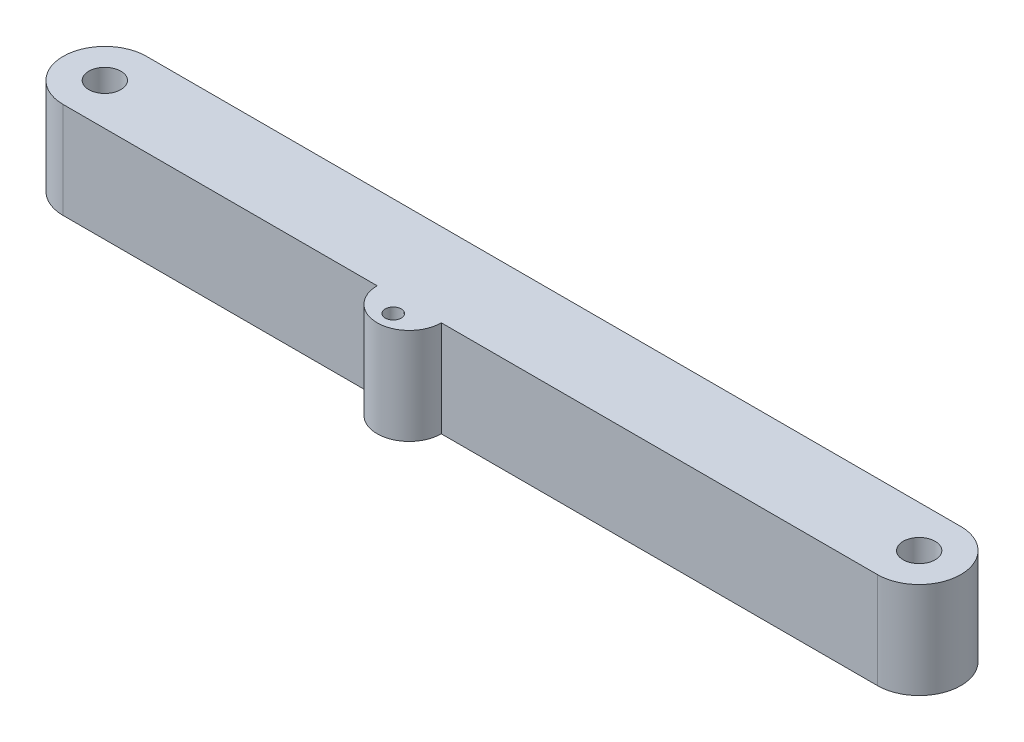
SolidWorks part; units mm, degrees
ref_plane "Front Plane" through (0, 0, 0) normal (0, 0, 1) x (1, 0, 0)
ref_plane "Top Plane" through (0, 0, 0) normal (0, 1, 0) x (1, 0, 0)
ref_plane "Right Plane" through (0, 0, 0) normal (1, 0, 0) x (0, 0, -1)
sketch "Sketch1" plane through (0, 0, 0) normal (0, 1, 0) x (1, 0, 0)
  line L0 (0, 0) -> (34315.2938, 0) construction
  line L1 (0, 0) -> (0, 34315.2938) construction
  line L2 (-80.645, -8.255) -> (80.645, -8.255)
  line L3 (-80.645, 8.255) -> (80.645, 8.255)
  arc A1 (-80.645, 8.255) -> (-80.645, -8.255) centre (-80.645, 0) ccw
  arc A2 (80.645, 8.255) -> (80.645, -8.255) centre (80.645, 0) cw
  circle A3 centre (-80.645, 0) radius 3.175
  circle A4 centre (80.645, 0) radius 3.175
  point P2 (-88.9, 0)
  point P7 (88.9, 0)
  point P13 (0, -8.255)
  point P16 (0, 8.255)
  dimension "D2" = 177.8
  dimension "D3" = 6.35
  dimension "D1" = 16.51
extrude "Boss-Extrude1" add sketch "Sketch1" along normal blind 19.05
sketch "Sketch2" plane through (0, 19.05, 0) normal (0, 1, 0) x (1, 0, 0)
  line L0 (0, 0) -> (50000, 0) construction
  line L1 (-12.0976, 0) -> (-12.0976, -8.255)
  line L2 (-80.645, -8.255) -> (80.645, -8.255)
  line L3 (80.645, 8.255) -> (-80.645, 8.255)
  line L4 (-80.645, -8.255) -> (80.645, -8.255)
  line L5 (80.645, 8.255) -> (-80.645, 8.255)
  line L6 (-12.0976, -14.605) -> (49987.9024, -14.605) construction
  circle A0 centre (-12.0976, -8.255) radius 6.35
  circle A1 centre (-12.0976, -11.43) radius 1.5875
  arc A2 (-80.645, 8.255) -> (-80.645, -8.255) centre (-80.645, 0) ccw
  arc A3 (80.645, -8.255) -> (80.645, 8.255) centre (80.645, 0) ccw
  arc A4 (-80.645, 8.255) -> (-80.645, -8.255) centre (-80.645, 0) ccw
  arc A5 (80.645, -8.255) -> (80.645, 8.255) centre (80.645, 0) ccw
  point P9 (-88.9, 0)
  point P16 (-12.0976, -14.605)
  line M8 (-80.645, -8.255) -> (80.645, -8.255)
  dimension "D3" = 12.7
  dimension "D4" = 3.175
  dimension "D5" = 3.175
  dimension "D2" = 76.8024
  dimension "D1" = 0
extrude "Boss-Extrude2" add sketch "Sketch2" along direction (0, 1, 0) on the side against the normal up to surface (19.05 mm away) contours L4 A0 L1 | L1 A0 M8
